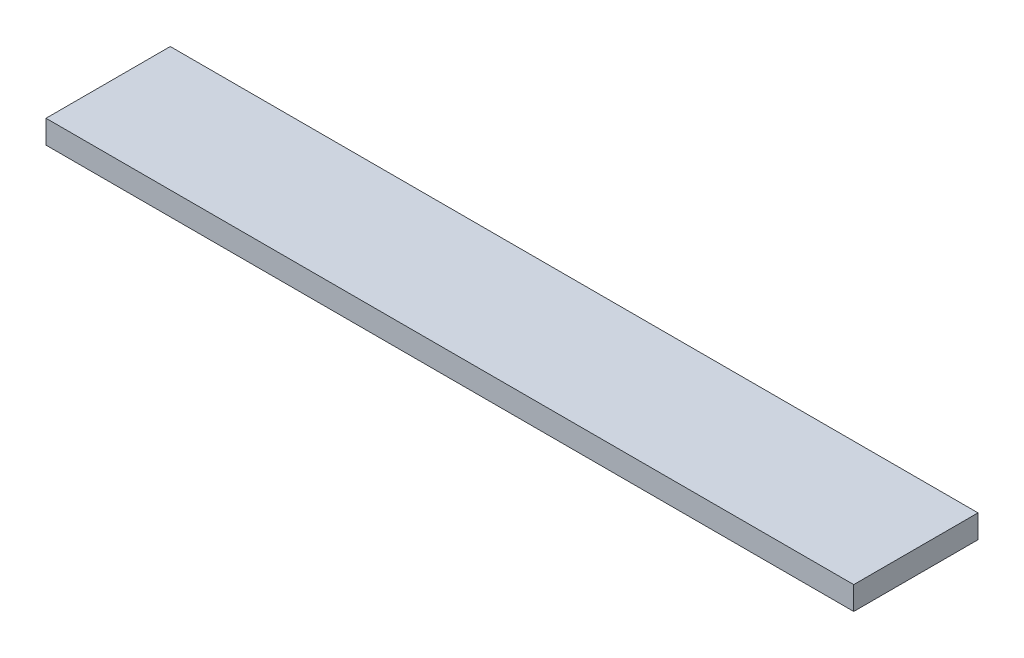
SolidWorks part; units mm, degrees
ref_plane "Front Plane" through (0, 0, 0) normal (0, 0, 1) x (1, 0, 0)
ref_plane "Top Plane" through (0, 0, 0) normal (0, 1, 0) x (1, 0, 0)
ref_plane "Right Plane" through (0, 0, 0) normal (1, 0, 0) x (0, 0, -1)
sketch "Sketch1" plane through (0, 0, 0) normal (0, 1, 0) x (1, 0, 0)
  line L1 (0, 0) -> (165.1, 0)
  line L2 (0, 0) -> (0, -25.4)
  line L3 (0, -25.4) -> (165.1, -25.4)
  line L4 (165.1, 0) -> (165.1, -25.4)
  dimension "D1" = 25.4
  dimension "D2" = 165.1
extrude "Boss-Extrude1" add sketch "Sketch1" along normal blind 4.7625 contours L1 L4 L3 L2
